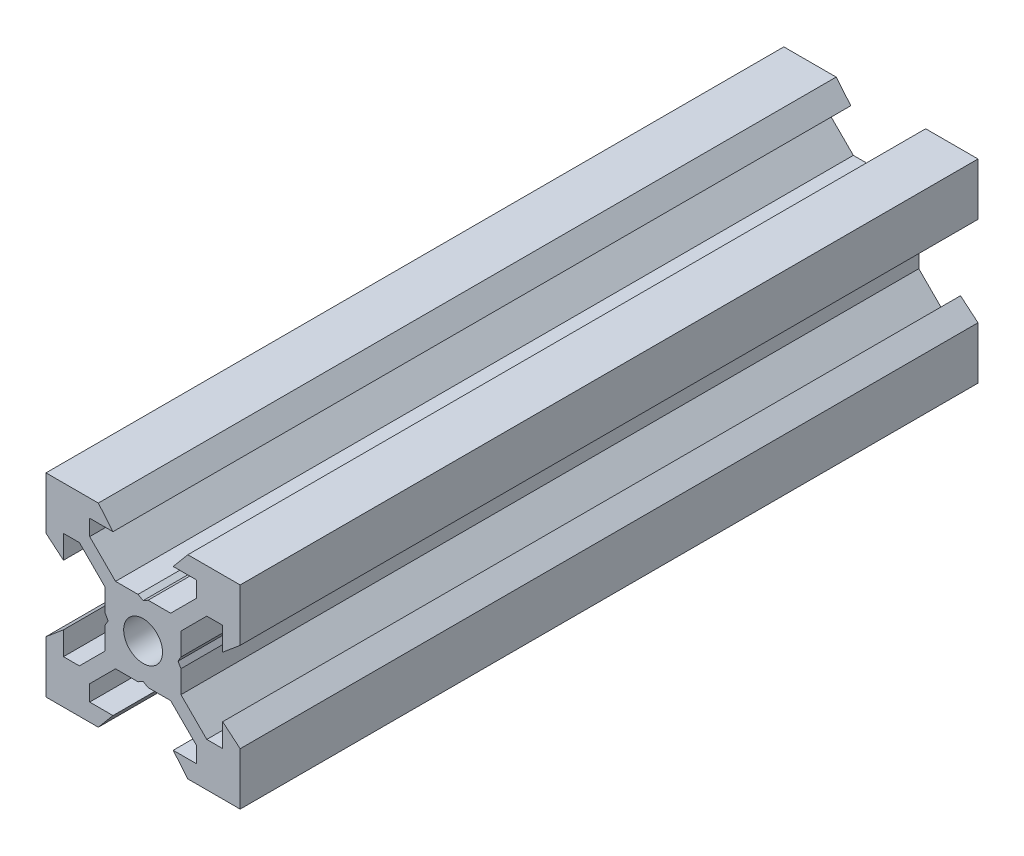
SolidWorks part; units mm, degrees
ref_plane "Front Plane" through (0, 0, 0) normal (0, 0, 1) x (1, 0, 0)
ref_plane "Top Plane" through (0, 0, 0) normal (0, 1, 0) x (1, 0, 0)
ref_plane "Right Plane" through (0, 0, 0) normal (1, 0, 0) x (0, 0, -1)
sketch "Sketch1" plane through (0, 0, 0) normal (0, 0, 1) x (1, 0, 0)
  line L0 (10, 10) -> (4.6104, 10) construction
  line L1 (10, 10) -> (10, 4.6104) construction
  line L2 (10, -10) -> (10, -4.6104) construction
  line L3 (10, -10) -> (4.6104, -10) construction
  line L4 (10, 10) -> (10, 4.6104)
  line L5 (6.5607, 5.5) -> (8.2, 5.5)
  line L6 (5.5, 8.2) -> (5.5, 6.5607)
  line L7 (10, 10) -> (4.6104, 10)
  line L8 (10, 10) -> (10, 4.6104)
  line L9 (6.5607, 5.5) -> (3.9, 2.8393)
  line L10 (5.5, 6.5607) -> (2.8393, 3.9)
  line L11 (10, 4.6104) -> (8.2, 3.1)
  line L12 (4.6104, 10) -> (3.1, 8.2)
  line L13 (8.2, 3.1) -> (8.2, 5.5)
  line L14 (3.1, 8.2) -> (5.5, 8.2)
  line L15 (-6.5607, 5.5) -> (-8.2, 5.5)
  line L16 (6.5607, -5.5) -> (8.2, -5.5)
  line L17 (3.1, -8.2) -> (5.5, -8.2)
  line L18 (8.2, -3.1) -> (8.2, -5.5)
  line L19 (4.6104, -10) -> (3.1, -8.2)
  line L20 (10, -4.6104) -> (8.2, -3.1)
  line L21 (0.5196, -3.9) -> (0, -3.6)
  line L22 (0.5196, 3.9) -> (0, 3.6)
  line L23 (3.6, 0) -> (3.9, -0.5196)
  line L24 (3.9, 0.5196) -> (3.6, 0)
  line L25 (3.9, 0.5196) -> (3.9, 2.8393)
  line L26 (2.8393, 3.9) -> (0.5196, 3.9)
  line L27 (3.9, -2.8393) -> (3.9, -0.5196)
  line L28 (2.8393, -3.9) -> (0.5196, -3.9)
  line L29 (5.5, -6.5607) -> (2.8393, -3.9)
  line L30 (6.5607, -5.5) -> (3.9, -2.8393)
  line L31 (10, -10) -> (10, -4.6104)
  line L32 (10, -10) -> (4.6104, -10)
  line L33 (5.5, -8.2) -> (5.5, -6.5607)
  line L34 (-6.5607, -5.5) -> (-8.2, -5.5)
  line L35 (10, -10) -> (10, -4.6104)
  line L36 (0, 0) -> (0, 8.2) construction
  line L37 (-10, -10) -> (-4.6104, -10) construction
  line L38 (-10, -10) -> (-10, -4.6104) construction
  line L39 (-10, 10) -> (-10, 4.6104) construction
  line L40 (-10, 10) -> (-4.6104, 10) construction
  line L41 (-10, -10) -> (-10, -4.6104)
  line L43 (-5.5, -8.2) -> (-5.5, -6.5607)
  line L44 (-10, -10) -> (-4.6104, -10)
  line L45 (-10, -10) -> (-10, -4.6104)
  line L46 (-6.5607, -5.5) -> (-3.9, -2.8393)
  line L47 (-5.5, -6.5607) -> (-2.8393, -3.9)
  line L48 (-2.8393, -3.9) -> (-0.5196, -3.9)
  line L49 (-3.9, -2.8393) -> (-3.9, -0.5196)
  line L50 (-2.8393, 3.9) -> (-0.5196, 3.9)
  line L51 (-3.9, 0.5196) -> (-3.9, 2.8393)
  line L52 (-3.9, 0.5196) -> (-3.6, 0)
  line L53 (-3.6, 0) -> (-3.9, -0.5196)
  line L54 (-0.5196, 3.9) -> (0, 3.6)
  line L55 (-0.5196, -3.9) -> (0, -3.6)
  line L56 (-10, -4.6104) -> (-8.2, -3.1)
  line L57 (-4.6104, -10) -> (-3.1, -8.2)
  line L58 (-8.2, -3.1) -> (-8.2, -5.5)
  line L59 (-3.1, -8.2) -> (-5.5, -8.2)
  line L60 (-10, -10) -> (10, -10) construction
  line L61 (-10, -10) -> (-10, 10) construction
  line L62 (-3.1, 8.2) -> (-5.5, 8.2)
  line L63 (-8.2, 3.1) -> (-8.2, 5.5)
  line L64 (-4.6104, 10) -> (-3.1, 8.2)
  line L65 (-10, 4.6104) -> (-8.2, 3.1)
  line L66 (-5.5, 6.5607) -> (-2.8393, 3.9)
  line L67 (-6.5607, 5.5) -> (-3.9, 2.8393)
  line L68 (-10, 10) -> (-10, 4.6104)
  line L69 (-10, 10) -> (-4.6104, 10)
  line L70 (-5.5, 8.2) -> (-5.5, 6.5607)
  line L71 (-10, 10) -> (10, 10) construction
  line L72 (-10, 10) -> (-10, 4.6104)
  line L73 (10, -10) -> (10, 10) construction
  line L74 (-10, -10) -> (10, 10) construction
  line L75 (-10, 10) -> (10, -10) construction
  circle A0 centre (0, 0) radius 2
  dimension "D7" = 4
  dimension "D1" = 20
  dimension "D2" = 5.3896
  dimension "D3" = 4.5
  dimension "D4" = 50
  dimension "D5" = 1.8
  dimension "D6" = 1.5104
  dimension "D8" = 5.5
  dimension "D9" = 120
  dimension "D10" = 0.3
  dimension "D11" = 2.3197
  dimension "D12" = 7.8
  dimension "D13" = 7.8
  dimension "D14" = 1.5
  dimension "D15" = 2.6607
extrude "Boss-Extrude1" add sketch "Sketch1" along normal mid plane 76 contours L70 L62 L64 L69 L68 L65 L63 L15 L67 L51 L52 L53 L49 L46 L34 L58 L56 L41 L44 L57 L59 L43 L47 L48 L55 L21 L28 L29 L33 L17 L19 L32 L31 L20 L18 L16 L30 L27 L23 L24 L25 L9 L5 L13 L11 L4 L7 L12 L14 L6 L10
